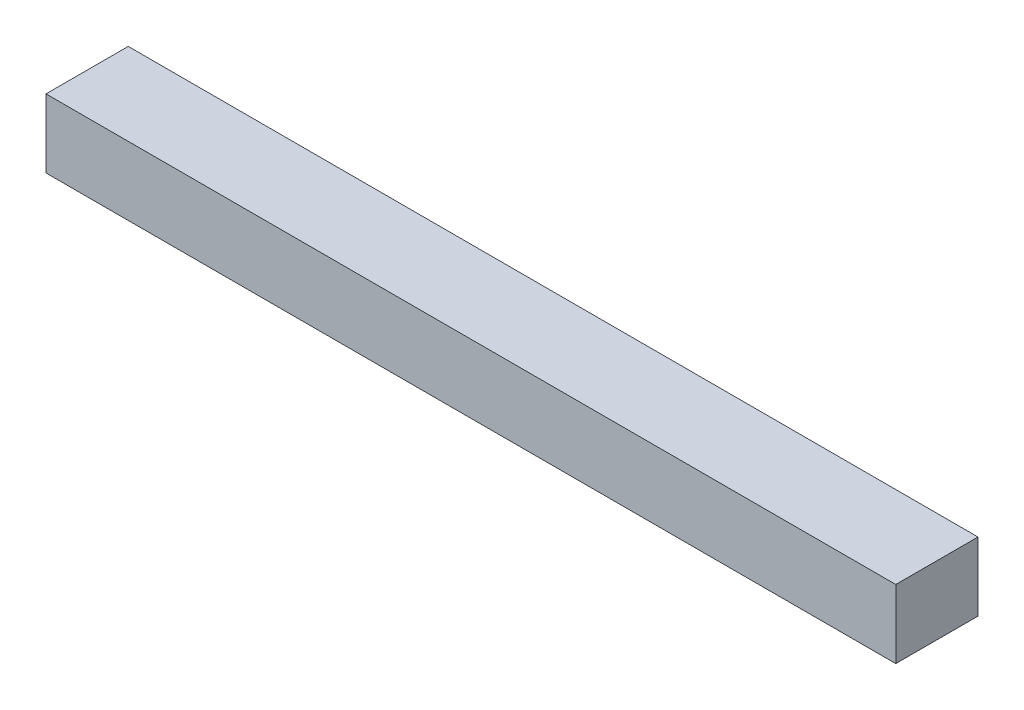
SolidWorks part; units mm, degrees
ref_plane "Спереди" through (0, 0, 0) normal (0, 0, 1) x (1, 0, 0)
ref_plane "Сверху" through (0, 0, 0) normal (0, 1, 0) x (1, 0, 0)
ref_plane "Справа" through (0, 0, 0) normal (1, 0, 0) x (0, 0, -1)
sketch "Эскиз2" plane through (0, 0, 0) normal (1, 0, 0) x (0, 0, -1)
  line L1 (-15, -12.5) -> (15, -12.5)
  line L2 (-15, -12.5) -> (-15, 12.5)
  line L3 (-15, 12.5) -> (15, 12.5)
  line L4 (15, -12.5) -> (15, 12.5)
  line L5 (-15, -12.5) -> (15, 12.5) construction
  line L6 (-15, 12.5) -> (15, -12.5) construction
  point P0 (0, 0)
extrude "Бобышка-Вытянуть1" add sketch "Эскиз2" along normal blind 310
